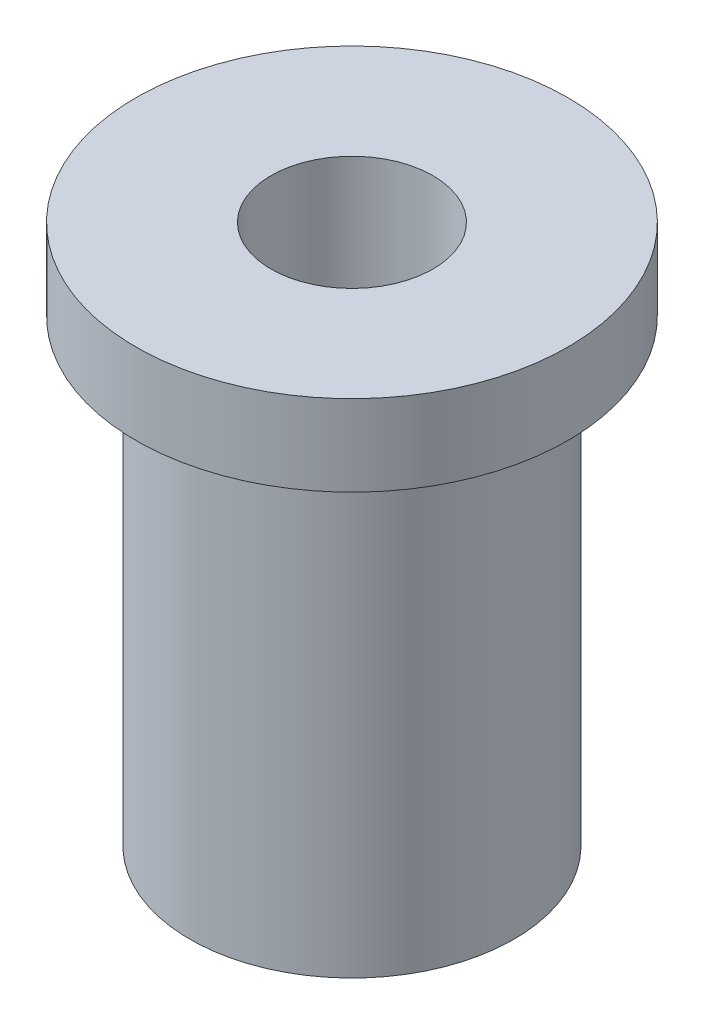
SolidWorks part; units mm, degrees
ref_plane "Plan de face" through (0, 0, 0) normal (0, 0, 1) x (1, 0, 0)
ref_plane "Plan de dessus" through (0, 0, 0) normal (0, 1, 0) x (1, 0, 0)
ref_plane "Plan de droite" through (0, 0, 0) normal (1, 0, 0) x (0, 0, -1)
sketch "Esquisse1" plane through (0, 0, 0) normal (0, 0, 1) x (1, 0, 0)
  line L0 (0, 0) -> (0, 54.9537) construction
  line L1 (3, 0) -> (3, 20)
  line L2 (3, 20) -> (8, 20)
  line L3 (8, 20) -> (8, 17)
  line L4 (8, 17) -> (6, 17)
  line L5 (6, 17) -> (6, 0)
  line L6 (6, 0) -> (3, 0)
  dimension "D1" = 3
  dimension "D2" = 6
  dimension "D3" = 8
  dimension "D4" = 20
  dimension "D5" = 17
revolve "Révolution1" add sketch "Esquisse1" angle 360 about L0
